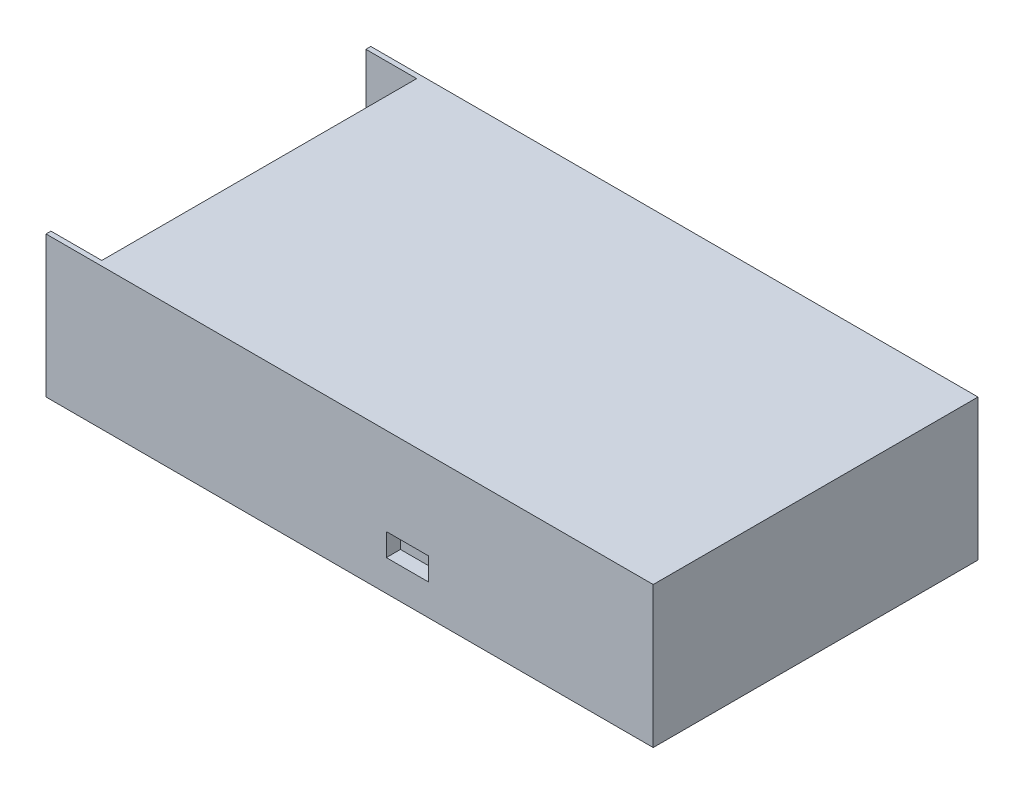
SolidWorks part; units mm, degrees
ref_plane "Front Plane" through (0, 0, 0) normal (0, 0, 1) x (1, 0, 0)
ref_plane "Top Plane" through (0, 0, 0) normal (0, 1, 0) x (1, 0, 0)
ref_plane "Right Plane" through (0, 0, 0) normal (1, 0, 0) x (0, 0, -1)
sketch "Sketch1" plane through (0, 0, 0) normal (0, 1, 0) x (1, 0, 0)
  line L0 (-107.5, 57.5) -> (107.5, -57.5) construction
  line L1 (-107.5, 57.5) -> (107.5, 57.5)
  line L2 (-107.5, 57.5) -> (-107.5, -57.5)
  line L3 (-107.5, -57.5) -> (107.5, -57.5)
  line L4 (107.5, 57.5) -> (107.5, -57.5)
  dimension "D1" = 115
  dimension "D2" = 215
extrude "Boss-Extrude1" add sketch "Sketch1" along normal blind 50
sketch "Sketch2" plane through (0, 50, 0) normal (0, 1, 0) x (1, 0, 0)
  line L0 (-107.5, 57.5) -> (-107.5, -57.5) construction
  line L1 (-107.5, 55.75) -> (-89.5, 55.75)
  line L2 (-107.5, 55.75) -> (-107.5, -55.75)
  line L3 (-107.5, -55.75) -> (-89.5, -55.75)
  line L4 (-89.5, 55.75) -> (-89.5, -55.75)
  line L5 (107.5, 57.5) -> (-107.5, 57.5) construction
  line L6 (-107.5, -57.5) -> (107.5, -57.5) construction
  dimension "D1" = 18
  dimension "D2" = 1.75
  dimension "D3" = 1.75
extrude "Cut-Extrude1" cut sketch "Sketch2" against normal offset from surface (41.25 mm away) 8.75 up to face at (0, 0, 0)
sketch "Sketch3" plane through (0, 0, 0) normal (0, -1, 0) x (1, 0, 0)
  line L0 (-107.5, 57.5) -> (107.5, 57.5) construction
  line L1 (-107.5, 55.75) -> (-107.5, -55.75) construction
  circle A0 centre (-75, -25) radius 2
  circle A1 centre (-75, 25) radius 2
  circle A2 centre (75, -25) radius 2
  circle A3 centre (75, 25) radius 2
  dimension "D5" = 4
  dimension "D1" = 32.5
  dimension "D2" = 50
  dimension "D3" = 150
  dimension "D4" = 32.5
extrude "Cut-Extrude2" cut sketch "Sketch3" against normal blind 5
sketch "Sketch4" plane through (0, 0, 57.5) normal (0, 0, 1) x (1, 0, 0)
  line L0 (-107.5, 0) -> (107.5, 0) construction
  line L1 (13, 19) -> (28, 19)
  line L2 (13, 19) -> (13, 11)
  line L3 (13, 11) -> (28, 11)
  line L4 (28, 19) -> (28, 11)
  line L5 (107.5, 50) -> (107.5, 0) construction
  dimension "D1" = 11
  dimension "D2" = 79.5
  dimension "D3" = 15
  dimension "D4" = 8
extrude "Cut-Extrude3" cut sketch "Sketch4" against normal blind 5
